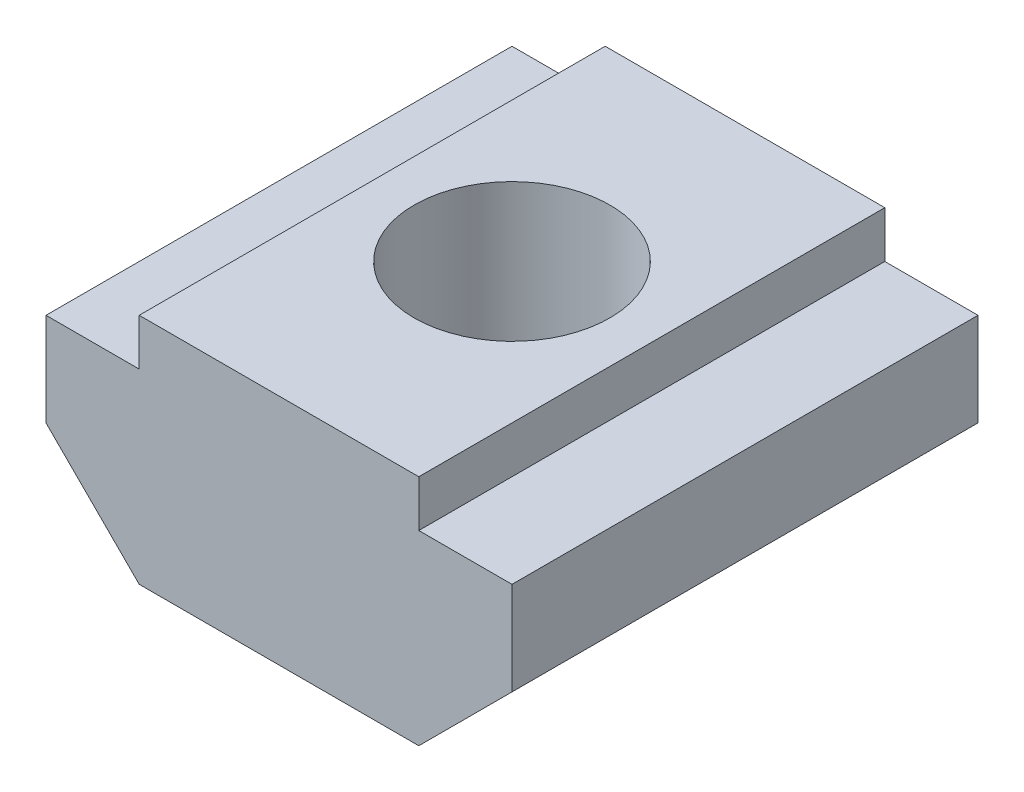
SolidWorks part; units mm, degrees
ref_plane "Front Plane" through (0, 0, 0) normal (0, 0, 1) x (1, 0, 0)
ref_plane "Top Plane" through (0, 0, 0) normal (0, 1, 0) x (1, 0, 0)
ref_plane "Right Plane" through (0, 0, 0) normal (1, 0, 0) x (0, 0, -1)
sketch "Sketch1" plane through (0, 0, 0) normal (0, 0, 1) x (1, 0, 0)
  line L0 (-5, -0.5) -> (-3, -2.5)
  line L1 (-3, -2.5) -> (3, -2.5)
  line L2 (-3, -2.5) -> (-3, 2.5)
  line L3 (-3, 2.5) -> (3, 2.5)
  line L4 (3, -2.5) -> (3, 2.5)
  line L5 (-3, -2.5) -> (3, 2.5) construction
  line L6 (-3, 2.5) -> (3, -2.5) construction
  line L7 (-5, -2.5) -> (5, -2.5)
  line L8 (-5, -2.5) -> (-5, 1.5)
  line L9 (-5, 1.5) -> (5, 1.5)
  line L10 (5, -2.5) -> (5, 1.5)
  line L11 (5, -0.5) -> (3, -2.5)
  line L12 (-5, -0.5) -> (5, -0.5) construction
  line L13 (0, -0.5) -> (0, 0) construction
  point P0 (0, 0)
  dimension "D1" = 6
  dimension "D2" = 5
  dimension "D3" = 10
  dimension "D4" = 4
  dimension "D5" = 6
  dimension "D6" = 45
extrude "Boss-Extrude1" add sketch "Sketch1" along normal mid plane 10 contours L9 L8 L0 L7 L2 | L9 L2 L1 L4 | L2 L9 L4 L3 | L11 L10 L9 L4 L7
sketch "Sketch2" plane through (0, 2.5, 0) normal (0, 1, 0) x (1, 0, 0)
  circle A0 centre (0, 0) radius 2.1
  dimension "D1" = 4.2
extrude "Cut-Extrude1" cut sketch "Sketch2" against normal through all
